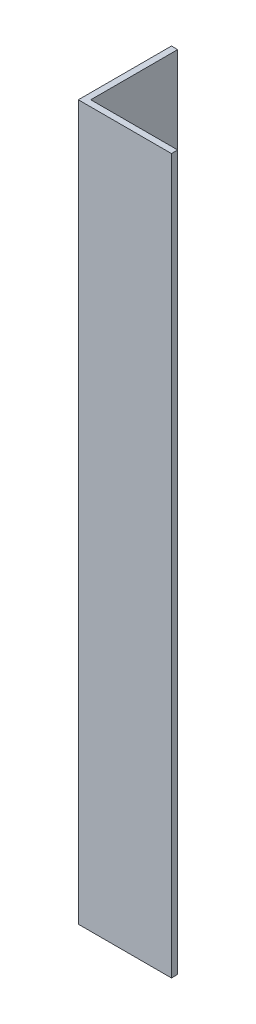
SolidWorks part; units mm, degrees
material "1060 Сплав"
ref_plane "Спереди" through (0, 0, 0) normal (0, 0, 1) x (1, 0, 0)
ref_plane "Сверху" through (0, 0, 0) normal (0, 1, 0) x (1, 0, 0)
ref_plane "Справа" through (0, 0, 0) normal (1, 0, 0) x (0, 0, -1)
sketch "Эскиз1" plane through (0, 0, 0) normal (0, 1, 0) x (1, 0, 0)
  line L0 (0, 0) -> (0, 15)
  line L1 (0, 15) -> (1, 15)
  line L2 (1, 15) -> (1, 1)
  line L3 (1, 1) -> (15, 1)
  line L4 (15, 1) -> (15, 0)
  line L5 (15, 0) -> (0, 0)
  dimension "D1" = 1
  dimension "D2" = 15
extrude "Бобышка-Вытянуть1" add sketch "Эскиз1" along normal blind 115
sketch "Эскиз2" plane through (0, 0, 0) normal (0, 0, 1) x (1, 0, 0)
  line L0 (7.5, 115) -> (7.5, 0) construction
  line L1 (0, 115) -> (15, 115) construction
  line L2 (0, 0) -> (15, 0) construction
